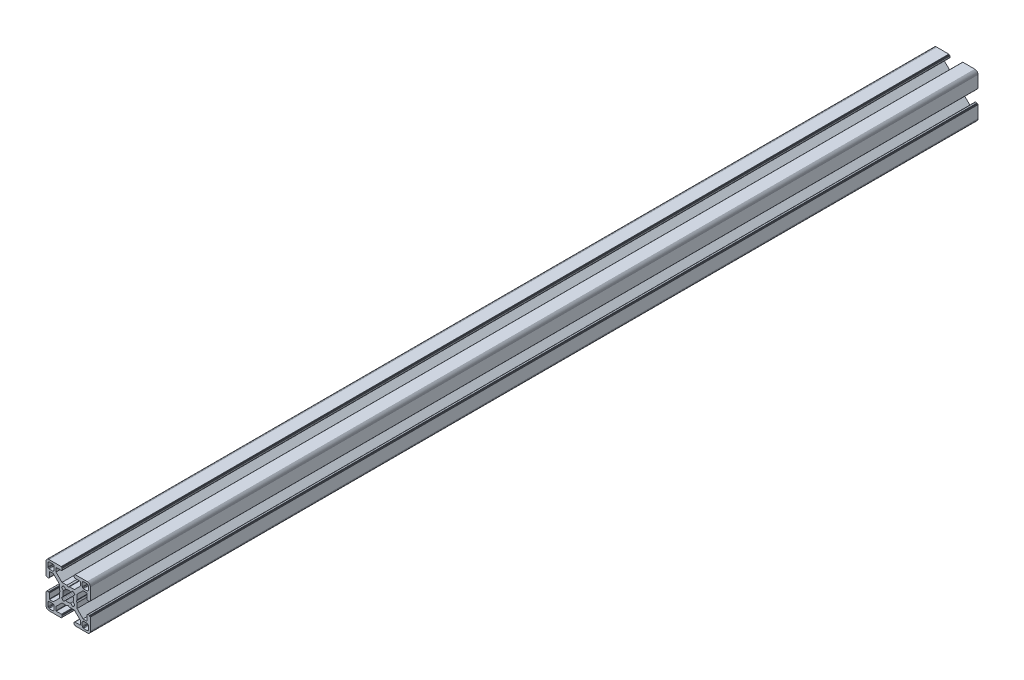
SolidWorks part; units mm, degrees
ref_plane "Front Plane" through (0, 0, 0) normal (0, 0, 1) x (1, 0, 0)
ref_plane "Top Plane" through (0, 0, 0) normal (0, 1, 0) x (1, 0, 0)
ref_plane "Right Plane" through (0, 0, 0) normal (1, 0, 0) x (0, 0, -1)
ref_plane "Plane1" through (0, 0, 0) normal (0, 0, 1) x (1, 0, 0)
sketch "Sketch1" plane through (0, 0, 0) normal (0, 0, 1) x (1, 0, 0)
  line L0 (28.3473, 29.9696) -> (28, 30)
  line L1 (28, 30) -> (19.75, 30)
  line L2 (19.75, 30) -> (19.7153, 29.997)
  line L3 (19.7153, 29.997) -> (19.6816, 29.9879)
  line L4 (19.6816, 29.9879) -> (19.65, 29.9732)
  line L5 (19.65, 29.9732) -> (19.6214, 29.9532)
  line L6 (19.6214, 29.9532) -> (19.5968, 29.9286)
  line L7 (19.5968, 29.9286) -> (19.5768, 29.9)
  line L8 (19.5768, 29.9) -> (19.5621, 29.8684)
  line L9 (19.5621, 29.8684) -> (19.553, 29.8347)
  line L10 (19.553, 29.8347) -> (19.55, 29.8)
  line L11 (19.55, 29.8) -> (19.55, 29.7)
  line L12 (19.55, 29.7) -> (19.547, 29.6653)
  line L13 (19.547, 29.6653) -> (19.5379, 29.6316)
  line L14 (19.5379, 29.6316) -> (19.5232, 29.6)
  line L15 (19.5232, 29.6) -> (19.5032, 29.5714)
  line L16 (19.5032, 29.5714) -> (19.4786, 29.5468)
  line L17 (19.4786, 29.5468) -> (19.45, 29.5268)
  line L18 (19.45, 29.5268) -> (19.4184, 29.5121)
  line L19 (19.4184, 29.5121) -> (19.3847, 29.503)
  line L20 (19.3847, 29.503) -> (19.35, 29.5)
  line L21 (19.35, 29.5) -> (19.25, 29.5)
  line L22 (19.25, 29.5) -> (19.2153, 29.497)
  line L23 (19.2153, 29.497) -> (19.1816, 29.4879)
  line L24 (19.1816, 29.4879) -> (19.15, 29.4732)
  line L25 (19.15, 29.4732) -> (19.1214, 29.4532)
  line L26 (19.1214, 29.4532) -> (19.0968, 29.4286)
  line L27 (19.0968, 29.4286) -> (19.0768, 29.4)
  line L28 (19.0768, 29.4) -> (19.0621, 29.3684)
  line L29 (19.0621, 29.3684) -> (19.053, 29.3347)
  line L30 (19.053, 29.3347) -> (19.05, 29.3)
  line L31 (19.05, 29.3) -> (19.05, 28.4)
  line L32 (19.05, 28.4) -> (19.0591, 28.2958)
  line L33 (19.0591, 28.2958) -> (19.0862, 28.1948)
  line L34 (19.0862, 28.1948) -> (19.1304, 28.1)
  line L35 (19.1304, 28.1) -> (19.1904, 28.0143)
  line L36 (19.1904, 28.0143) -> (19.2643, 27.9404)
  line L37 (19.2643, 27.9404) -> (19.35, 27.8804)
  line L38 (19.35, 27.8804) -> (19.4448, 27.8362)
  line L39 (19.4448, 27.8362) -> (19.5458, 27.8091)
  line L40 (19.5458, 27.8091) -> (19.65, 27.8)
  line L41 (19.65, 27.8) -> (23.05, 27.8)
  line L42 (23.05, 27.8) -> (23.0847, 27.7969)
  line L43 (23.0847, 27.7969) -> (23.1184, 27.7879)
  line L44 (23.1184, 27.7879) -> (23.15, 27.7732)
  line L45 (23.15, 27.7732) -> (23.1786, 27.7532)
  line L46 (23.1786, 27.7532) -> (23.2032, 27.7285)
  line L47 (23.2032, 27.7285) -> (23.2232, 27.7)
  line L48 (23.2232, 27.7) -> (23.2379, 27.6684)
  line L49 (23.2379, 27.6684) -> (23.247, 27.6347)
  line L50 (23.247, 27.6347) -> (23.25, 27.6)
  line L51 (23.25, 27.6) -> (23.25, 25.05)
  line L52 (23.25, 25.05) -> (19.2045, 21)
  line L53 (19.2045, 21) -> (15.9, 21)
  line L54 (15.9, 21) -> (15, 20.4848)
  line L55 (15, 20.4848) -> (14.1, 21)
  line L56 (14.1, 21) -> (10.7955, 21)
  line L57 (10.7955, 21) -> (7.9973, 23.8013)
  line L58 (7.9973, 23.8013) -> (6.75, 25.05)
  line L59 (6.75, 25.05) -> (6.75, 27.6)
  line L60 (6.75, 27.6) -> (6.753, 27.6347)
  line L61 (6.753, 27.6347) -> (6.7621, 27.6684)
  line L62 (6.7621, 27.6684) -> (6.7768, 27.7)
  line L63 (6.7768, 27.7) -> (6.7968, 27.7285)
  line L64 (6.7968, 27.7285) -> (6.8215, 27.7532)
  line L65 (6.8215, 27.7532) -> (6.85, 27.7732)
  line L66 (6.85, 27.7732) -> (6.8816, 27.7879)
  line L67 (6.8816, 27.7879) -> (6.9153, 27.7969)
  line L68 (6.9153, 27.7969) -> (6.95, 27.8)
  line L69 (6.95, 27.8) -> (10.35, 27.8)
  line L70 (10.35, 27.8) -> (10.4542, 27.8091)
  line L71 (10.4542, 27.8091) -> (10.5552, 27.8362)
  line L72 (10.5552, 27.8362) -> (10.65, 27.8804)
  line L73 (10.65, 27.8804) -> (10.7357, 27.9404)
  line L74 (10.7357, 27.9404) -> (10.8096, 28.0143)
  line L75 (10.8096, 28.0143) -> (10.8696, 28.1)
  line L76 (10.8696, 28.1) -> (10.9138, 28.1948)
  line L77 (10.9138, 28.1948) -> (10.9409, 28.2958)
  line L78 (10.9409, 28.2958) -> (10.95, 28.4)
  line L79 (10.95, 28.4) -> (10.95, 29.3)
  line L80 (10.95, 29.3) -> (10.947, 29.3347)
  line L81 (10.947, 29.3347) -> (10.938, 29.3684)
  line L82 (10.938, 29.3684) -> (10.9232, 29.4)
  line L83 (10.9232, 29.4) -> (10.9032, 29.4286)
  line L84 (10.9032, 29.4286) -> (10.8786, 29.4532)
  line L85 (10.8786, 29.4532) -> (10.85, 29.4732)
  line L86 (10.85, 29.4732) -> (10.8184, 29.4879)
  line L87 (10.8184, 29.4879) -> (10.7847, 29.497)
  line L88 (10.7847, 29.497) -> (10.75, 29.5)
  line L89 (10.75, 29.5) -> (10.65, 29.5)
  line L90 (10.65, 29.5) -> (10.6153, 29.503)
  line L91 (10.6153, 29.503) -> (10.5816, 29.5121)
  line L92 (10.5816, 29.5121) -> (10.55, 29.5268)
  line L93 (10.55, 29.5268) -> (10.5214, 29.5468)
  line L94 (10.5214, 29.5468) -> (10.4968, 29.5714)
  line L95 (10.4968, 29.5714) -> (10.4768, 29.6)
  line L96 (10.4768, 29.6) -> (10.4621, 29.6316)
  line L97 (10.4621, 29.6316) -> (10.453, 29.6653)
  line L98 (10.453, 29.6653) -> (10.45, 29.7)
  line L99 (10.45, 29.7) -> (10.45, 29.8)
  line L100 (10.45, 29.8) -> (10.447, 29.8347)
  line L101 (10.447, 29.8347) -> (10.4379, 29.8684)
  line L102 (10.4379, 29.8684) -> (10.4232, 29.9)
  line L103 (10.4232, 29.9) -> (10.4032, 29.9286)
  line L104 (10.4032, 29.9286) -> (10.3786, 29.9532)
  line L105 (10.3786, 29.9532) -> (10.35, 29.9732)
  line L106 (10.35, 29.9732) -> (10.3184, 29.9879)
  line L107 (10.3184, 29.9879) -> (10.2847, 29.997)
  line L108 (10.2847, 29.997) -> (10.25, 30)
  line L109 (10.25, 30) -> (2, 30)
  line L110 (2, 30) -> (1.6527, 29.9696)
  line L111 (1.6527, 29.9696) -> (1.316, 29.8794)
  line L112 (1.316, 29.8794) -> (1, 29.7321)
  line L113 (1, 29.7321) -> (0.7144, 29.5321)
  line L114 (0.7144, 29.5321) -> (0.4679, 29.2856)
  line L115 (0.4679, 29.2856) -> (0.2679, 29)
  line L116 (0.2679, 29) -> (0.1206, 28.684)
  line L117 (0.1206, 28.684) -> (0.0304, 28.3473)
  line L118 (0.0304, 28.3473) -> (0, 28)
  line L119 (0, 28) -> (0, 19.75)
  line L120 (0, 19.75) -> (0.003, 19.7153)
  line L121 (0.003, 19.7153) -> (0.0121, 19.6816)
  line L122 (0.0121, 19.6816) -> (0.0268, 19.65)
  line L123 (0.0268, 19.65) -> (0.0468, 19.6214)
  line L124 (0.0468, 19.6214) -> (0.0714, 19.5968)
  line L125 (0.0714, 19.5968) -> (0.1, 19.5768)
  line L126 (0.1, 19.5768) -> (0.1316, 19.5621)
  line L127 (0.1316, 19.5621) -> (0.1653, 19.553)
  line L128 (0.1653, 19.553) -> (0.2, 19.55)
  line L129 (0.2, 19.55) -> (0.3, 19.55)
  line L130 (0.3, 19.55) -> (0.3347, 19.547)
  line L131 (0.3347, 19.547) -> (0.3684, 19.5379)
  line L132 (0.3684, 19.5379) -> (0.4, 19.5232)
  line L133 (0.4, 19.5232) -> (0.4286, 19.5032)
  line L134 (0.4286, 19.5032) -> (0.4532, 19.4786)
  line L135 (0.4532, 19.4786) -> (0.4732, 19.45)
  line L136 (0.4732, 19.45) -> (0.4879, 19.4184)
  line L137 (0.4879, 19.4184) -> (0.497, 19.3847)
  line L138 (0.497, 19.3847) -> (0.5, 19.35)
  line L139 (0.5, 19.35) -> (0.5, 19.25)
  line L140 (0.5, 19.25) -> (0.503, 19.2153)
  line L141 (0.503, 19.2153) -> (0.5121, 19.1816)
  line L142 (0.5121, 19.1816) -> (0.5268, 19.15)
  line L143 (0.5268, 19.15) -> (0.5468, 19.1214)
  line L144 (0.5468, 19.1214) -> (0.5714, 19.0968)
  line L145 (0.5714, 19.0968) -> (0.6, 19.0768)
  line L146 (0.6, 19.0768) -> (0.6316, 19.0621)
  line L147 (0.6316, 19.0621) -> (0.6653, 19.053)
  line L148 (0.6653, 19.053) -> (0.7, 19.05)
  line L149 (0.7, 19.05) -> (1.6, 19.05)
  line L150 (1.6, 19.05) -> (1.7042, 19.0591)
  line L151 (1.7042, 19.0591) -> (1.8052, 19.0862)
  line L152 (1.8052, 19.0862) -> (1.9, 19.1304)
  line L153 (1.9, 19.1304) -> (1.9857, 19.1904)
  line L154 (1.9857, 19.1904) -> (2.0596, 19.2643)
  line L155 (2.0596, 19.2643) -> (2.1196, 19.35)
  line L156 (2.1196, 19.35) -> (2.1638, 19.4448)
  line L157 (2.1638, 19.4448) -> (2.1909, 19.5458)
  line L158 (2.1909, 19.5458) -> (2.2, 19.65)
  line L159 (2.2, 19.65) -> (2.2, 23.05)
  line L160 (2.2, 23.05) -> (2.203, 23.0847)
  line L161 (2.203, 23.0847) -> (2.2121, 23.1184)
  line L162 (2.2121, 23.1184) -> (2.2268, 23.15)
  line L163 (2.2268, 23.15) -> (2.2468, 23.1786)
  line L164 (2.2468, 23.1786) -> (2.2714, 23.2032)
  line L165 (2.2714, 23.2032) -> (2.3, 23.2232)
  line L166 (2.3, 23.2232) -> (2.3316, 23.2379)
  line L167 (2.3316, 23.2379) -> (2.3653, 23.247)
  line L168 (2.3653, 23.247) -> (2.4, 23.25)
  line L169 (2.4, 23.25) -> (4.95, 23.25)
  line L170 (4.95, 23.25) -> (7.9973, 20.2027)
  line L171 (7.9973, 20.2027) -> (8.9955, 19.2045)
  line L172 (8.9955, 19.2045) -> (8.9955, 15.9)
  line L173 (8.9955, 15.9) -> (9.5151, 15)
  line L174 (9.5151, 15) -> (8.9955, 14.1)
  line L175 (8.9955, 14.1) -> (8.9955, 10.7955)
  line L176 (8.9955, 10.7955) -> (4.95, 6.75)
  line L177 (4.95, 6.75) -> (2.4, 6.75)
  line L178 (2.4, 6.75) -> (2.3653, 6.753)
  line L179 (2.3653, 6.753) -> (2.3316, 6.7621)
  line L180 (2.3316, 6.7621) -> (2.3, 6.7768)
  line L181 (2.3, 6.7768) -> (2.2714, 6.7968)
  line L182 (2.2714, 6.7968) -> (2.2468, 6.8214)
  line L183 (2.2468, 6.8214) -> (2.2268, 6.85)
  line L184 (2.2268, 6.85) -> (2.2121, 6.8816)
  line L185 (2.2121, 6.8816) -> (2.203, 6.9153)
  line L186 (2.203, 6.9153) -> (2.2, 6.95)
  line L187 (2.2, 6.95) -> (2.2, 10.35)
  line L188 (2.2, 10.35) -> (2.1909, 10.4542)
  line L189 (2.1909, 10.4542) -> (2.1638, 10.5552)
  line L190 (2.1638, 10.5552) -> (2.1196, 10.65)
  line L191 (2.1196, 10.65) -> (2.0596, 10.7357)
  line L192 (2.0596, 10.7357) -> (1.9857, 10.8096)
  line L193 (1.9857, 10.8096) -> (1.9, 10.8696)
  line L194 (1.9, 10.8696) -> (1.8052, 10.9138)
  line L195 (1.8052, 10.9138) -> (1.7042, 10.9409)
  line L196 (1.7042, 10.9409) -> (1.6, 10.95)
  line L197 (1.6, 10.95) -> (0.7, 10.95)
  line L198 (0.7, 10.95) -> (0.6653, 10.9469)
  line L199 (0.6653, 10.9469) -> (0.6316, 10.9379)
  line L200 (0.6316, 10.9379) -> (0.6, 10.9232)
  line L201 (0.6, 10.9232) -> (0.5715, 10.9032)
  line L202 (0.5715, 10.9032) -> (0.5468, 10.8785)
  line L203 (0.5468, 10.8785) -> (0.5268, 10.85)
  line L204 (0.5268, 10.85) -> (0.5121, 10.8184)
  line L205 (0.5121, 10.8184) -> (0.503, 10.7847)
  line L206 (0.503, 10.7847) -> (0.5, 10.75)
  line L207 (0.5, 10.75) -> (0.5, 10.65)
  line L208 (0.5, 10.65) -> (0.497, 10.6153)
  line L209 (0.497, 10.6153) -> (0.4879, 10.5816)
  line L210 (0.4879, 10.5816) -> (0.4732, 10.55)
  line L211 (0.4732, 10.55) -> (0.4532, 10.5214)
  line L212 (0.4532, 10.5214) -> (0.4286, 10.4968)
  line L213 (0.4286, 10.4968) -> (0.4, 10.4768)
  line L214 (0.4, 10.4768) -> (0.3684, 10.4621)
  line L215 (0.3684, 10.4621) -> (0.3347, 10.453)
  line L216 (0.3347, 10.453) -> (0.3, 10.45)
  line L217 (0.3, 10.45) -> (0.2, 10.45)
  line L218 (0.2, 10.45) -> (0.1653, 10.447)
  line L219 (0.1653, 10.447) -> (0.1316, 10.4379)
  line L220 (0.1316, 10.4379) -> (0.1, 10.4232)
  line L221 (0.1, 10.4232) -> (0.0714, 10.4032)
  line L222 (0.0714, 10.4032) -> (0.0468, 10.3786)
  line L223 (0.0468, 10.3786) -> (0.0268, 10.35)
  line L224 (0.0268, 10.35) -> (0.0121, 10.3184)
  line L225 (0.0121, 10.3184) -> (0.003, 10.2847)
  line L226 (0.003, 10.2847) -> (0, 10.25)
  line L227 (0, 10.25) -> (0, 2)
  line L228 (0, 2) -> (0.0304, 1.6527)
  line L229 (0.0304, 1.6527) -> (0.1206, 1.316)
  line L230 (0.1206, 1.316) -> (0.2679, 1)
  line L231 (0.2679, 1) -> (0.4679, 0.7144)
  line L232 (0.4679, 0.7144) -> (0.7144, 0.4679)
  line L233 (0.7144, 0.4679) -> (1, 0.2679)
  line L234 (1, 0.2679) -> (1.316, 0.1206)
  line L235 (1.316, 0.1206) -> (1.6527, 0.0304)
  line L236 (1.6527, 0.0304) -> (2, 0)
  line L237 (2, 0) -> (10.25, 0)
  line L238 (10.25, 0) -> (10.2847, 0.003)
  line L239 (10.2847, 0.003) -> (10.3184, 0.0121)
  line L240 (10.3184, 0.0121) -> (10.35, 0.0268)
  line L241 (10.35, 0.0268) -> (10.3786, 0.0468)
  line L242 (10.3786, 0.0468) -> (10.4032, 0.0714)
  line L243 (10.4032, 0.0714) -> (10.4232, 0.1)
  line L244 (10.4232, 0.1) -> (10.4379, 0.1316)
  line L245 (10.4379, 0.1316) -> (10.447, 0.1653)
  line L246 (10.447, 0.1653) -> (10.45, 0.2)
  line L247 (10.45, 0.2) -> (10.45, 0.3)
  line L248 (10.45, 0.3) -> (10.453, 0.3347)
  line L249 (10.453, 0.3347) -> (10.4621, 0.3684)
  line L250 (10.4621, 0.3684) -> (10.4768, 0.4)
  line L251 (10.4768, 0.4) -> (10.4968, 0.4286)
  line L252 (10.4968, 0.4286) -> (10.5214, 0.4532)
  line L253 (10.5214, 0.4532) -> (10.55, 0.4732)
  line L254 (10.55, 0.4732) -> (10.5816, 0.4879)
  line L255 (10.5816, 0.4879) -> (10.6153, 0.497)
  line L256 (10.6153, 0.497) -> (10.65, 0.5)
  line L257 (10.65, 0.5) -> (10.75, 0.5)
  line L258 (10.75, 0.5) -> (10.7847, 0.503)
  line L259 (10.7847, 0.503) -> (10.8184, 0.5121)
  line L260 (10.8184, 0.5121) -> (10.85, 0.5268)
  line L261 (10.85, 0.5268) -> (10.8785, 0.5468)
  line L262 (10.8785, 0.5468) -> (10.9032, 0.5715)
  line L263 (10.9032, 0.5715) -> (10.9232, 0.6)
  line L264 (10.9232, 0.6) -> (10.9379, 0.6316)
  line L265 (10.9379, 0.6316) -> (10.9469, 0.6653)
  line L266 (10.9469, 0.6653) -> (10.95, 0.7)
  line L267 (10.95, 0.7) -> (10.95, 1.6)
  line L268 (10.95, 1.6) -> (10.9409, 1.7042)
  line L269 (10.9409, 1.7042) -> (10.9138, 1.8052)
  line L270 (10.9138, 1.8052) -> (10.8696, 1.9)
  line L271 (10.8696, 1.9) -> (10.8096, 1.9857)
  line L272 (10.8096, 1.9857) -> (10.7357, 2.0596)
  line L273 (10.7357, 2.0596) -> (10.65, 2.1196)
  line L274 (10.65, 2.1196) -> (10.5552, 2.1638)
  line L275 (10.5552, 2.1638) -> (10.4542, 2.1909)
  line L276 (10.4542, 2.1909) -> (10.35, 2.2)
  line L277 (10.35, 2.2) -> (6.95, 2.2)
  line L278 (6.95, 2.2) -> (6.9153, 2.203)
  line L279 (6.9153, 2.203) -> (6.8816, 2.212)
  line L280 (6.8816, 2.212) -> (6.85, 2.2268)
  line L281 (6.85, 2.2268) -> (6.8215, 2.2468)
  line L282 (6.8215, 2.2468) -> (6.7968, 2.2714)
  line L283 (6.7968, 2.2714) -> (6.7768, 2.3)
  line L284 (6.7768, 2.3) -> (6.7621, 2.3316)
  line L285 (6.7621, 2.3316) -> (6.753, 2.3653)
  line L286 (6.753, 2.3653) -> (6.75, 2.4)
  line L287 (6.75, 2.4) -> (6.75, 4.95)
  line L288 (6.75, 4.95) -> (9.7875, 7.9908)
  line L289 (9.7875, 7.9908) -> (10.7955, 9)
  line L290 (10.7955, 9) -> (14.1, 9)
  line L291 (14.1, 9) -> (15, 9.5151)
  line L292 (15, 9.5151) -> (15.9, 9)
  line L293 (15.9, 9) -> (19.2045, 9)
  line L294 (19.2045, 9) -> (20.2126, 7.9908)
  line L295 (20.2126, 7.9908) -> (23.25, 4.95)
  line L296 (23.25, 4.95) -> (23.25, 2.4)
  line L297 (23.25, 2.4) -> (23.247, 2.3653)
  line L298 (23.247, 2.3653) -> (23.2379, 2.3316)
  line L299 (23.2379, 2.3316) -> (23.2232, 2.3)
  line L300 (23.2232, 2.3) -> (23.2032, 2.2714)
  line L301 (23.2032, 2.2714) -> (23.1786, 2.2468)
  line L302 (23.1786, 2.2468) -> (23.15, 2.2268)
  line L303 (23.15, 2.2268) -> (23.1184, 2.212)
  line L304 (23.1184, 2.212) -> (23.0847, 2.203)
  line L305 (23.0847, 2.203) -> (23.05, 2.2)
  line L306 (23.05, 2.2) -> (19.65, 2.2)
  line L307 (19.65, 2.2) -> (19.5458, 2.1909)
  line L308 (19.5458, 2.1909) -> (19.4448, 2.1638)
  line L309 (19.4448, 2.1638) -> (19.35, 2.1196)
  line L310 (19.35, 2.1196) -> (19.2643, 2.0596)
  line L311 (19.2643, 2.0596) -> (19.1904, 1.9857)
  line L312 (19.1904, 1.9857) -> (19.1304, 1.9)
  line L313 (19.1304, 1.9) -> (19.0862, 1.8052)
  line L314 (19.0862, 1.8052) -> (19.0591, 1.7042)
  line L315 (19.0591, 1.7042) -> (19.05, 1.6)
  line L316 (19.05, 1.6) -> (19.05, 0.7)
  line L317 (19.05, 0.7) -> (19.053, 0.6653)
  line L318 (19.053, 0.6653) -> (19.0621, 0.6316)
  line L319 (19.0621, 0.6316) -> (19.0768, 0.6)
  line L320 (19.0768, 0.6) -> (19.0968, 0.5714)
  line L321 (19.0968, 0.5714) -> (19.1214, 0.5468)
  line L322 (19.1214, 0.5468) -> (19.15, 0.5268)
  line L323 (19.15, 0.5268) -> (19.1816, 0.5121)
  line L324 (19.1816, 0.5121) -> (19.2153, 0.503)
  line L325 (19.2153, 0.503) -> (19.25, 0.5)
  line L326 (19.25, 0.5) -> (19.35, 0.5)
  line L327 (19.35, 0.5) -> (19.3847, 0.497)
  line L328 (19.3847, 0.497) -> (19.4184, 0.4879)
  line L329 (19.4184, 0.4879) -> (19.45, 0.4732)
  line L330 (19.45, 0.4732) -> (19.4786, 0.4532)
  line L331 (19.4786, 0.4532) -> (19.5032, 0.4286)
  line L332 (19.5032, 0.4286) -> (19.5232, 0.4)
  line L333 (19.5232, 0.4) -> (19.5379, 0.3684)
  line L334 (19.5379, 0.3684) -> (19.547, 0.3347)
  line L335 (19.547, 0.3347) -> (19.55, 0.3)
  line L336 (19.55, 0.3) -> (19.55, 0.2)
  line L337 (19.55, 0.2) -> (19.553, 0.1653)
  line L338 (19.553, 0.1653) -> (19.5621, 0.1316)
  line L339 (19.5621, 0.1316) -> (19.5768, 0.1)
  line L340 (19.5768, 0.1) -> (19.5968, 0.0714)
  line L341 (19.5968, 0.0714) -> (19.6214, 0.0468)
  line L342 (19.6214, 0.0468) -> (19.65, 0.0268)
  line L343 (19.65, 0.0268) -> (19.6816, 0.0121)
  line L344 (19.6816, 0.0121) -> (19.7153, 0.003)
  line L345 (19.7153, 0.003) -> (19.75, 0)
  line L346 (19.75, 0) -> (28, 0)
  line L347 (28, 0) -> (28.3473, 0.0304)
  line L348 (28.3473, 0.0304) -> (28.684, 0.1206)
  line L349 (28.684, 0.1206) -> (29, 0.2679)
  line L350 (29, 0.2679) -> (29.2856, 0.4679)
  line L351 (29.2856, 0.4679) -> (29.5321, 0.7144)
  line L352 (29.5321, 0.7144) -> (29.7321, 1)
  line L353 (29.7321, 1) -> (29.8794, 1.316)
  line L354 (29.8794, 1.316) -> (29.9696, 1.6527)
  line L355 (29.9696, 1.6527) -> (30, 2)
  line L356 (30, 2) -> (30, 10.25)
  line L357 (30, 10.25) -> (29.997, 10.2847)
  line L358 (29.997, 10.2847) -> (29.988, 10.3184)
  line L359 (29.988, 10.3184) -> (29.9732, 10.35)
  line L360 (29.9732, 10.35) -> (29.9532, 10.3785)
  line L361 (29.9532, 10.3785) -> (29.9286, 10.4032)
  line L362 (29.9286, 10.4032) -> (29.9, 10.4232)
  line L363 (29.9, 10.4232) -> (29.8684, 10.4379)
  line L364 (29.8684, 10.4379) -> (29.8347, 10.447)
  line L365 (29.8347, 10.447) -> (29.8, 10.45)
  line L366 (29.8, 10.45) -> (29.7, 10.45)
  line L367 (29.7, 10.45) -> (29.6649, 10.4534)
  line L368 (29.6649, 10.4534) -> (29.6312, 10.4624)
  line L369 (29.6312, 10.4624) -> (29.5996, 10.4772)
  line L370 (29.5996, 10.4772) -> (29.5711, 10.4972)
  line L371 (29.5711, 10.4972) -> (29.5464, 10.5218)
  line L372 (29.5464, 10.5218) -> (29.5264, 10.5504)
  line L373 (29.5264, 10.5504) -> (29.5117, 10.582)
  line L374 (29.5117, 10.582) -> (29.5027, 10.6156)
  line L375 (29.5027, 10.6156) -> (29.4996, 10.6504)
  line L376 (29.4996, 10.6504) -> (29.4996, 10.7504)
  line L377 (29.4996, 10.7504) -> (29.497, 10.7847)
  line L378 (29.497, 10.7847) -> (29.4879, 10.8184)
  line L379 (29.4879, 10.8184) -> (29.4732, 10.85)
  line L380 (29.4732, 10.85) -> (29.4532, 10.8785)
  line L381 (29.4532, 10.8785) -> (29.4286, 10.9032)
  line L382 (29.4286, 10.9032) -> (29.4, 10.9232)
  line L383 (29.4, 10.9232) -> (29.3684, 10.9379)
  line L384 (29.3684, 10.9379) -> (29.3347, 10.9469)
  line L385 (29.3347, 10.9469) -> (29.3, 10.95)
  line L386 (29.3, 10.95) -> (28.4, 10.95)
  line L387 (28.4, 10.95) -> (28.2958, 10.9409)
  line L388 (28.2958, 10.9409) -> (28.1948, 10.9138)
  line L389 (28.1948, 10.9138) -> (28.1, 10.8696)
  line L390 (28.1, 10.8696) -> (28.0143, 10.8096)
  line L391 (28.0143, 10.8096) -> (27.9404, 10.7357)
  line L392 (27.9404, 10.7357) -> (27.8804, 10.65)
  line L393 (27.8804, 10.65) -> (27.8362, 10.5552)
  line L394 (27.8362, 10.5552) -> (27.8091, 10.4542)
  line L395 (27.8091, 10.4542) -> (27.8, 10.35)
  line L396 (27.8, 10.35) -> (27.8, 6.95)
  line L397 (27.8, 6.95) -> (27.797, 6.9153)
  line L398 (27.797, 6.9153) -> (27.7879, 6.8816)
  line L399 (27.7879, 6.8816) -> (27.7732, 6.85)
  line L400 (27.7732, 6.85) -> (27.7532, 6.8214)
  line L401 (27.7532, 6.8214) -> (27.7286, 6.7968)
  line L402 (27.7286, 6.7968) -> (27.7, 6.7768)
  line L403 (27.7, 6.7768) -> (27.6684, 6.7621)
  line L404 (27.6684, 6.7621) -> (27.6347, 6.753)
  line L405 (27.6347, 6.753) -> (27.6, 6.75)
  line L406 (27.6, 6.75) -> (25.05, 6.75)
  line L407 (25.05, 6.75) -> (23.8092, 7.9908)
  line L408 (23.8092, 7.9908) -> (21.0045, 10.7955)
  line L409 (21.0045, 10.7955) -> (21.0045, 14.1)
  line L410 (21.0045, 14.1) -> (20.4849, 15)
  line L411 (20.4849, 15) -> (21.0045, 15.9)
  line L412 (21.0045, 15.9) -> (21.0045, 19.2045)
  line L413 (21.0045, 19.2045) -> (25.05, 23.25)
  line L414 (25.05, 23.25) -> (27.6, 23.25)
  line L415 (27.6, 23.25) -> (27.6347, 23.247)
  line L416 (27.6347, 23.247) -> (27.6684, 23.2379)
  line L417 (27.6684, 23.2379) -> (27.7, 23.2232)
  line L418 (27.7, 23.2232) -> (27.7286, 23.2032)
  line L419 (27.7286, 23.2032) -> (27.7532, 23.1786)
  line L420 (27.7532, 23.1786) -> (27.7732, 23.15)
  line L421 (27.7732, 23.15) -> (27.7879, 23.1184)
  line L422 (27.7879, 23.1184) -> (27.797, 23.0847)
  line L423 (27.797, 23.0847) -> (27.8, 23.05)
  line L424 (27.8, 23.05) -> (27.8, 19.65)
  line L425 (27.8, 19.65) -> (27.8091, 19.5458)
  line L426 (27.8091, 19.5458) -> (27.8362, 19.4448)
  line L427 (27.8362, 19.4448) -> (27.8804, 19.35)
  line L428 (27.8804, 19.35) -> (27.9404, 19.2643)
  line L429 (27.9404, 19.2643) -> (28.0143, 19.1904)
  line L430 (28.0143, 19.1904) -> (28.1, 19.1304)
  line L431 (28.1, 19.1304) -> (28.1948, 19.0862)
  line L432 (28.1948, 19.0862) -> (28.2958, 19.0591)
  line L433 (28.2958, 19.0591) -> (28.4, 19.05)
  line L434 (28.4, 19.05) -> (29.3, 19.05)
  line L435 (29.3, 19.05) -> (29.3347, 19.053)
  line L436 (29.3347, 19.053) -> (29.3684, 19.0621)
  line L437 (29.3684, 19.0621) -> (29.4, 19.0768)
  line L438 (29.4, 19.0768) -> (29.4282, 19.0971)
  line L439 (29.4282, 19.0971) -> (29.4528, 19.1218)
  line L440 (29.4528, 19.1218) -> (29.4728, 19.1504)
  line L441 (29.4728, 19.1504) -> (29.4876, 19.182)
  line L442 (29.4876, 19.182) -> (29.4966, 19.2156)
  line L443 (29.4966, 19.2156) -> (29.4996, 19.2504)
  line L444 (29.4996, 19.2504) -> (29.4996, 19.3504)
  line L445 (29.4996, 19.3504) -> (29.5027, 19.3851)
  line L446 (29.5027, 19.3851) -> (29.5117, 19.4188)
  line L447 (29.5117, 19.4188) -> (29.5264, 19.4504)
  line L448 (29.5264, 19.4504) -> (29.5464, 19.4789)
  line L449 (29.5464, 19.4789) -> (29.5711, 19.5036)
  line L450 (29.5711, 19.5036) -> (29.5996, 19.5236)
  line L451 (29.5996, 19.5236) -> (29.6312, 19.5383)
  line L452 (29.6312, 19.5383) -> (29.6649, 19.5473)
  line L453 (29.6649, 19.5473) -> (29.7, 19.55)
  line L454 (29.7, 19.55) -> (29.8, 19.55)
  line L455 (29.8, 19.55) -> (29.8347, 19.553)
  line L456 (29.8347, 19.553) -> (29.8684, 19.5621)
  line L457 (29.8684, 19.5621) -> (29.9, 19.5768)
  line L458 (29.9, 19.5768) -> (29.9286, 19.5968)
  line L459 (29.9286, 19.5968) -> (29.9532, 19.6214)
  line L460 (29.9532, 19.6214) -> (29.9732, 19.65)
  line L461 (29.9732, 19.65) -> (29.9879, 19.6816)
  line L462 (29.9879, 19.6816) -> (29.997, 19.7153)
  line L463 (29.997, 19.7153) -> (30, 19.75)
  line L464 (30, 19.75) -> (30, 28)
  line L465 (30, 28) -> (29.9696, 28.3473)
  line L466 (29.9696, 28.3473) -> (29.8794, 28.684)
  line L467 (29.8794, 28.684) -> (29.7321, 29)
  line L468 (29.7321, 29) -> (29.5321, 29.2856)
  line L469 (29.5321, 29.2856) -> (29.2856, 29.5321)
  line L470 (29.2856, 29.5321) -> (29, 29.7321)
  line L471 (29, 29.7321) -> (28.684, 29.8794)
  line L472 (28.684, 29.8794) -> (28.3473, 29.9696)
  line L473 (1.3, 25.5) -> (1.3, 27.7)
  line L474 (1.3, 27.7) -> (1.3123, 27.8564)
  line L475 (1.3123, 27.8564) -> (1.3489, 28.009)
  line L476 (1.3489, 28.009) -> (1.409, 28.154)
  line L477 (1.409, 28.154) -> (1.491, 28.2878)
  line L478 (1.491, 28.2878) -> (1.5929, 28.4071)
  line L479 (1.5929, 28.4071) -> (1.7122, 28.509)
  line L480 (1.7122, 28.509) -> (1.846, 28.591)
  line L481 (1.846, 28.591) -> (1.991, 28.6511)
  line L482 (1.991, 28.6511) -> (2.1436, 28.6877)
  line L483 (2.1436, 28.6877) -> (2.3, 28.7)
  line L484 (2.3, 28.7) -> (4.5, 28.7)
  line L485 (4.5, 28.7) -> (4.6564, 28.6877)
  line L486 (4.6564, 28.6877) -> (4.809, 28.6511)
  line L487 (4.809, 28.6511) -> (4.954, 28.591)
  line L488 (4.954, 28.591) -> (5.0878, 28.509)
  line L489 (5.0878, 28.509) -> (5.2071, 28.4071)
  line L490 (5.2071, 28.4071) -> (5.309, 28.2878)
  line L491 (5.309, 28.2878) -> (5.391, 28.154)
  line L492 (5.391, 28.154) -> (5.4511, 28.009)
  line L493 (5.4511, 28.009) -> (5.4877, 27.8564)
  line L494 (5.4877, 27.8564) -> (5.5, 27.7)
  line L495 (5.5, 27.7) -> (5.5, 25.5)
  line L496 (5.5, 25.5) -> (5.4877, 25.3436)
  line L497 (5.4877, 25.3436) -> (5.4511, 25.191)
  line L498 (5.4511, 25.191) -> (5.391, 25.046)
  line L499 (5.391, 25.046) -> (5.309, 24.9122)
  line L500 (5.309, 24.9122) -> (5.2071, 24.7929)
  line L501 (5.2071, 24.7929) -> (5.0878, 24.691)
  line L502 (5.0878, 24.691) -> (4.954, 24.609)
  line L503 (4.954, 24.609) -> (4.809, 24.5489)
  line L504 (4.809, 24.5489) -> (4.6564, 24.5123)
  line L505 (4.6564, 24.5123) -> (4.5, 24.5)
  line L506 (4.5, 24.5) -> (2.3, 24.5)
  line L507 (2.3, 24.5) -> (2.1436, 24.5123)
  line L508 (2.1436, 24.5123) -> (1.991, 24.5489)
  line L509 (1.991, 24.5489) -> (1.846, 24.609)
  line L510 (1.846, 24.609) -> (1.7122, 24.691)
  line L511 (1.7122, 24.691) -> (1.5929, 24.7929)
  line L512 (1.5929, 24.7929) -> (1.491, 24.9122)
  line L513 (1.491, 24.9122) -> (1.409, 25.046)
  line L514 (1.409, 25.046) -> (1.3489, 25.191)
  line L515 (1.3489, 25.191) -> (1.3123, 25.3436)
  line L516 (1.3123, 25.3436) -> (1.3, 25.5)
  line L517 (25.3436, 28.6877) -> (25.5, 28.7)
  line L518 (25.5, 28.7) -> (27.7, 28.7)
  line L519 (27.7, 28.7) -> (27.8564, 28.6877)
  line L520 (27.8564, 28.6877) -> (28.009, 28.6511)
  line L521 (28.009, 28.6511) -> (28.154, 28.591)
  line L522 (28.154, 28.591) -> (28.2878, 28.509)
  line L523 (28.2878, 28.509) -> (28.4071, 28.4071)
  line L524 (28.4071, 28.4071) -> (28.509, 28.2878)
  line L525 (28.509, 28.2878) -> (28.591, 28.154)
  line L526 (28.591, 28.154) -> (28.6511, 28.009)
  line L527 (28.6511, 28.009) -> (28.6877, 27.8564)
  line L528 (28.6877, 27.8564) -> (28.7, 27.7)
  line L529 (28.7, 27.7) -> (28.7, 25.5)
  line L530 (28.7, 25.5) -> (28.6877, 25.3436)
  line L531 (28.6877, 25.3436) -> (28.6511, 25.191)
  line L532 (28.6511, 25.191) -> (28.591, 25.046)
  line L533 (28.591, 25.046) -> (28.509, 24.9122)
  line L534 (28.509, 24.9122) -> (28.4071, 24.7929)
  line L535 (28.4071, 24.7929) -> (28.2878, 24.691)
  line L536 (28.2878, 24.691) -> (28.154, 24.609)
  line L537 (28.154, 24.609) -> (28.009, 24.5489)
  line L538 (28.009, 24.5489) -> (27.8564, 24.5123)
  line L539 (27.8564, 24.5123) -> (27.7, 24.5)
  line L540 (27.7, 24.5) -> (25.5, 24.5)
  line L541 (25.5, 24.5) -> (25.3436, 24.5123)
  line L542 (25.3436, 24.5123) -> (25.191, 24.5489)
  line L543 (25.191, 24.5489) -> (25.046, 24.609)
  line L544 (25.046, 24.609) -> (24.9122, 24.691)
  line L545 (24.9122, 24.691) -> (24.7929, 24.7929)
  line L546 (24.7929, 24.7929) -> (24.691, 24.9122)
  line L547 (24.691, 24.9122) -> (24.609, 25.046)
  line L548 (24.609, 25.046) -> (24.5489, 25.191)
  line L549 (24.5489, 25.191) -> (24.5123, 25.3436)
  line L550 (24.5123, 25.3436) -> (24.5, 25.5)
  line L551 (24.5, 25.5) -> (24.5, 27.7)
  line L552 (24.5, 27.7) -> (24.5123, 27.8564)
  line L553 (24.5123, 27.8564) -> (24.5489, 28.009)
  line L554 (24.5489, 28.009) -> (24.609, 28.154)
  line L555 (24.609, 28.154) -> (24.691, 28.2878)
  line L556 (24.691, 28.2878) -> (24.7929, 28.4071)
  line L557 (24.7929, 28.4071) -> (24.9122, 28.509)
  line L558 (24.9122, 28.509) -> (25.046, 28.591)
  line L559 (25.046, 28.591) -> (25.191, 28.6511)
  line L560 (25.191, 28.6511) -> (25.3436, 28.6877)
  line L561 (15, 18.65) -> (15.55, 18.6083)
  line L562 (15.55, 18.6083) -> (16.0875, 18.4842)
  line L563 (16.0875, 18.4842) -> (16.6001, 18.2806)
  line L564 (16.6001, 18.2806) -> (18.1359, 19.5184)
  line L565 (18.1359, 19.5184) -> (18.645, 19.1187)
  line L566 (18.645, 19.1187) -> (19.1036, 18.6621)
  line L567 (19.1036, 18.6621) -> (19.5053, 18.1547)
  line L568 (19.5053, 18.1547) -> (18.2806, 16.6001)
  line L569 (18.2806, 16.6001) -> (18.4842, 16.0875)
  line L570 (18.4842, 16.0875) -> (18.6083, 15.55)
  line L571 (18.6083, 15.55) -> (18.65, 15)
  line L572 (18.65, 15) -> (18.6083, 14.45)
  line L573 (18.6083, 14.45) -> (18.4842, 13.9125)
  line L574 (18.4842, 13.9125) -> (18.2806, 13.3999)
  line L575 (18.2806, 13.3999) -> (19.5053, 11.8453)
  line L576 (19.5053, 11.8453) -> (19.1036, 11.3379)
  line L577 (19.1036, 11.3379) -> (18.645, 10.8813)
  line L578 (18.645, 10.8813) -> (18.1359, 10.4816)
  line L579 (18.1359, 10.4816) -> (16.6001, 11.7194)
  line L580 (16.6001, 11.7194) -> (16.0875, 11.5158)
  line L581 (16.0875, 11.5158) -> (15.55, 11.3917)
  line L582 (15.55, 11.3917) -> (15, 11.35)
  line L583 (15, 11.35) -> (14.45, 11.3917)
  line L584 (14.45, 11.3917) -> (13.9125, 11.5158)
  line L585 (13.9125, 11.5158) -> (13.3999, 11.7194)
  line L586 (13.3999, 11.7194) -> (11.8641, 10.4816)
  line L587 (11.8641, 10.4816) -> (11.355, 10.8813)
  line L588 (11.355, 10.8813) -> (10.8964, 11.3379)
  line L589 (10.8964, 11.3379) -> (10.4947, 11.8453)
  line L590 (10.4947, 11.8453) -> (11.7194, 13.3999)
  line L591 (11.7194, 13.3999) -> (11.5158, 13.9125)
  line L592 (11.5158, 13.9125) -> (11.3917, 14.45)
  line L593 (11.3917, 14.45) -> (11.35, 15)
  line L594 (11.35, 15) -> (11.3917, 15.55)
  line L595 (11.3917, 15.55) -> (11.5158, 16.0875)
  line L596 (11.5158, 16.0875) -> (11.7194, 16.6001)
  line L597 (11.7194, 16.6001) -> (10.4947, 18.1547)
  line L598 (10.4947, 18.1547) -> (10.8964, 18.6621)
  line L599 (10.8964, 18.6621) -> (11.355, 19.1187)
  line L600 (11.355, 19.1187) -> (11.8641, 19.5184)
  line L601 (11.8641, 19.5184) -> (13.3999, 18.2806)
  line L602 (13.3999, 18.2806) -> (13.9125, 18.4842)
  line L603 (13.9125, 18.4842) -> (14.45, 18.6083)
  line L604 (14.45, 18.6083) -> (15, 18.65)
  line L605 (4.5, 1.3) -> (2.3, 1.3)
  line L606 (2.3, 1.3) -> (2.1436, 1.3123)
  line L607 (2.1436, 1.3123) -> (1.991, 1.3489)
  line L608 (1.991, 1.3489) -> (1.846, 1.409)
  line L609 (1.846, 1.409) -> (1.7122, 1.491)
  line L610 (1.7122, 1.491) -> (1.5929, 1.5929)
  line L611 (1.5929, 1.5929) -> (1.491, 1.7122)
  line L612 (1.491, 1.7122) -> (1.409, 1.846)
  line L613 (1.409, 1.846) -> (1.3489, 1.991)
  line L614 (1.3489, 1.991) -> (1.3123, 2.1436)
  line L615 (1.3123, 2.1436) -> (1.3, 2.3)
  line L616 (1.3, 2.3) -> (1.3, 4.5)
  line L617 (1.3, 4.5) -> (1.3123, 4.6564)
  line L618 (1.3123, 4.6564) -> (1.3489, 4.809)
  line L619 (1.3489, 4.809) -> (1.409, 4.954)
  line L620 (1.409, 4.954) -> (1.491, 5.0878)
  line L621 (1.491, 5.0878) -> (1.5929, 5.2071)
  line L622 (1.5929, 5.2071) -> (1.7122, 5.309)
  line L623 (1.7122, 5.309) -> (1.846, 5.391)
  line L624 (1.846, 5.391) -> (1.991, 5.4511)
  line L625 (1.991, 5.4511) -> (2.1436, 5.4877)
  line L626 (2.1436, 5.4877) -> (2.3, 5.5)
  line L627 (2.3, 5.5) -> (4.5, 5.5)
  line L628 (4.5, 5.5) -> (4.6564, 5.4877)
  line L629 (4.6564, 5.4877) -> (4.809, 5.4511)
  line L630 (4.809, 5.4511) -> (4.954, 5.391)
  line L631 (4.954, 5.391) -> (5.0878, 5.309)
  line L632 (5.0878, 5.309) -> (5.2071, 5.2071)
  line L633 (5.2071, 5.2071) -> (5.309, 5.0878)
  line L634 (5.309, 5.0878) -> (5.391, 4.954)
  line L635 (5.391, 4.954) -> (5.4511, 4.809)
  line L636 (5.4511, 4.809) -> (5.4877, 4.6564)
  line L637 (5.4877, 4.6564) -> (5.5, 4.5)
  line L638 (5.5, 4.5) -> (5.5, 2.3)
  line L639 (5.5, 2.3) -> (5.4877, 2.1436)
  line L640 (5.4877, 2.1436) -> (5.4511, 1.991)
  line L641 (5.4511, 1.991) -> (5.391, 1.846)
  line L642 (5.391, 1.846) -> (5.309, 1.7122)
  line L643 (5.309, 1.7122) -> (5.2071, 1.5929)
  line L644 (5.2071, 1.5929) -> (5.0878, 1.491)
  line L645 (5.0878, 1.491) -> (4.954, 1.409)
  line L646 (4.954, 1.409) -> (4.809, 1.3489)
  line L647 (4.809, 1.3489) -> (4.6564, 1.3123)
  line L648 (4.6564, 1.3123) -> (4.5, 1.3)
  line L649 (27.7, 1.3) -> (25.5, 1.3)
  line L650 (25.5, 1.3) -> (25.3436, 1.3123)
  line L651 (25.3436, 1.3123) -> (25.191, 1.3489)
  line L652 (25.191, 1.3489) -> (25.046, 1.409)
  line L653 (25.046, 1.409) -> (24.9122, 1.491)
  line L654 (24.9122, 1.491) -> (24.7929, 1.5929)
  line L655 (24.7929, 1.5929) -> (24.691, 1.7122)
  line L656 (24.691, 1.7122) -> (24.609, 1.846)
  line L657 (24.609, 1.846) -> (24.5489, 1.991)
  line L658 (24.5489, 1.991) -> (24.5123, 2.1436)
  line L659 (24.5123, 2.1436) -> (24.5, 2.3)
  line L660 (24.5, 2.3) -> (24.5, 4.5)
  line L661 (24.5, 4.5) -> (24.5123, 4.6564)
  line L662 (24.5123, 4.6564) -> (24.5489, 4.809)
  line L663 (24.5489, 4.809) -> (24.609, 4.954)
  line L664 (24.609, 4.954) -> (24.691, 5.0878)
  line L665 (24.691, 5.0878) -> (24.7929, 5.2071)
  line L666 (24.7929, 5.2071) -> (24.9122, 5.309)
  line L667 (24.9122, 5.309) -> (25.046, 5.391)
  line L668 (25.046, 5.391) -> (25.191, 5.4511)
  line L669 (25.191, 5.4511) -> (25.3436, 5.4877)
  line L670 (25.3436, 5.4877) -> (25.5, 5.5)
  line L671 (25.5, 5.5) -> (27.7, 5.5)
  line L672 (27.7, 5.5) -> (27.8564, 5.4877)
  line L673 (27.8564, 5.4877) -> (28.009, 5.4511)
  line L674 (28.009, 5.4511) -> (28.154, 5.391)
  line L675 (28.154, 5.391) -> (28.2878, 5.309)
  line L676 (28.2878, 5.309) -> (28.4071, 5.2071)
  line L677 (28.4071, 5.2071) -> (28.509, 5.0878)
  line L678 (28.509, 5.0878) -> (28.591, 4.954)
  line L679 (28.591, 4.954) -> (28.6511, 4.809)
  line L680 (28.6511, 4.809) -> (28.6877, 4.6564)
  line L681 (28.6877, 4.6564) -> (28.7, 4.5)
  line L682 (28.7, 4.5) -> (28.7, 2.3)
  line L683 (28.7, 2.3) -> (28.6877, 2.1436)
  line L684 (28.6877, 2.1436) -> (28.6511, 1.991)
  line L685 (28.6511, 1.991) -> (28.591, 1.846)
  line L686 (28.591, 1.846) -> (28.509, 1.7122)
  line L687 (28.509, 1.7122) -> (28.4071, 1.5929)
  line L688 (28.4071, 1.5929) -> (28.2878, 1.491)
  line L689 (28.2878, 1.491) -> (28.154, 1.409)
  line L690 (28.154, 1.409) -> (28.009, 1.3489)
  line L691 (28.009, 1.3489) -> (27.8564, 1.3123)
  line L692 (27.8564, 1.3123) -> (27.7, 1.3)
extrude "Boss-Extrude1" add sketch "Sketch1" against normal blind 600
